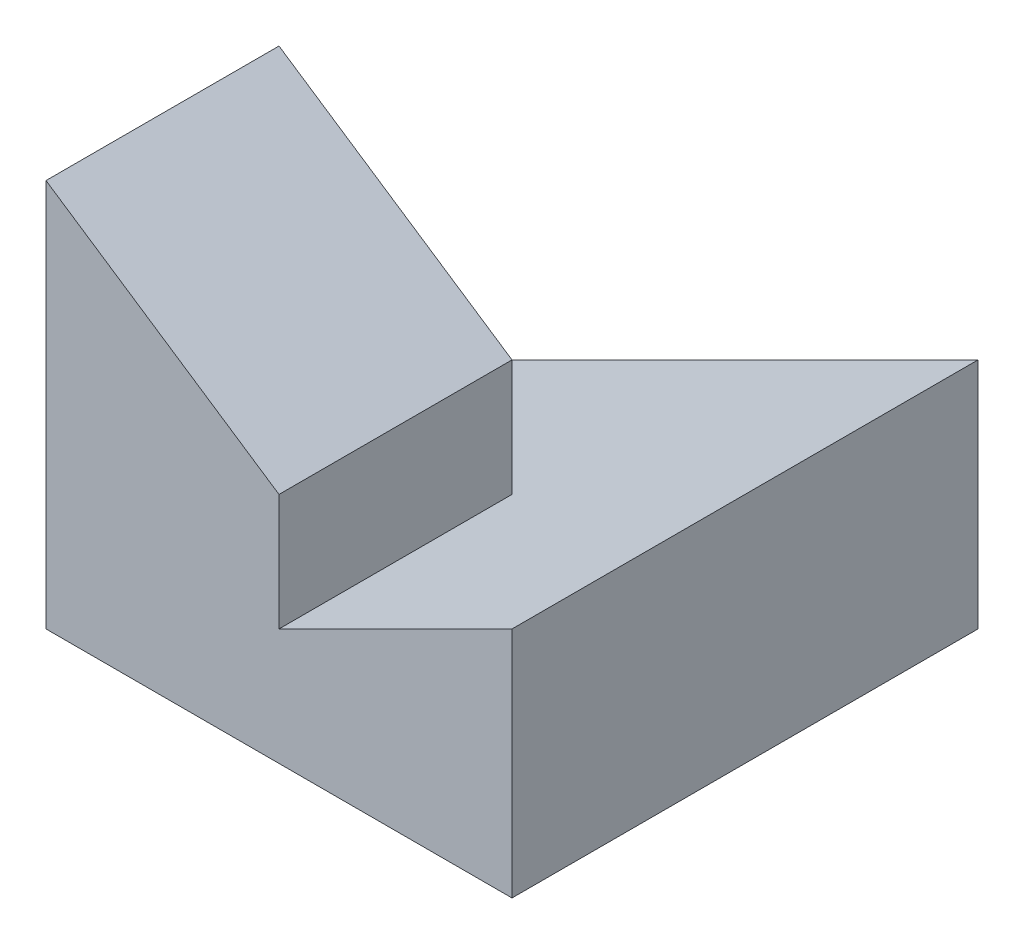
SolidWorks part; units mm, degrees
ref_plane "Front" through (0, 0, 0) normal (0, 0, 1) x (1, 0, 0)
ref_plane "Top" through (0, 0, 0) normal (0, 1, 0) x (1, 0, 0)
ref_plane "Right" through (0, 0, 0) normal (1, 0, 0) x (0, 0, -1)
sketch "Sketch1" plane through (0, 0, 0) normal (0, 1, 0) x (1, 0, 0)
  line L1 (-3, -3) -> (3, -3)
  line L2 (-3, -3) -> (-3, 3)
  line L3 (-3, 3) -> (3, 3)
  line L4 (3, -3) -> (3, 3)
  line L5 (-3, -3) -> (3, 3) construction
  line L6 (-3, 3) -> (3, -3) construction
  point P0 (0, 0)
  dimension "D1" = 6
  dimension "D2" = 6
extrude "Boss-Extrude1" add sketch "Sketch1" along normal blind 5
sketch "Sketch8" plane through (0, 0, 3) normal (0, 0, 1) x (1, 0, 0)
  line L0 (3, 3) -> (0, 1.5)
  line L1 (3, 5) -> (3, 0) construction
  line L2 (0, 1.5) -> (0, 3)
  line L3 (0, 3) -> (-3, 5)
  line L4 (-3, 5) -> (3, 5)
  line L5 (3, 5) -> (3, 3)
  dimension "D1" = 2
  dimension "D2" = 3
  dimension "D3" = 1.5
  dimension "D4" = 1.5
extrude "Cut-Extrude5" cut sketch "Sketch8" against normal blind 3
sketch "Sketch9" plane through (0, 0, -3) normal (0, 0, -1) x (-1, 0, 0)
  line L0 (-3, 3) -> (0, 1.5)
  line L1 (0, 1.5) -> (3, 0)
  line L2 (3, 5) -> (3, 0) construction
  line L7 (-3, 0) -> (3, 0)
  line L8 (3, 0) -> (3, 5)
  line L9 (3, 5) -> (-3, 5)
  line L10 (-3, 5) -> (-3, 0)
  line L11 (-3, 0) -> (3, 0)
  line L12 (3, 0) -> (3, 5)
  line L13 (3, 5) -> (-3, 5)
  line L14 (-3, 5) -> (-3, 0)
  line M6 (3, 0) -> (3, 5)
  line M7 (3, 5) -> (-3, 5)
  line M8 (-3, 5) -> (-3, 0)
  dimension "D1" = 0
extrude "Cut-Extrude6" cut sketch "Sketch9" against normal blind 3 contours L0 L1 M6 M7 M8
